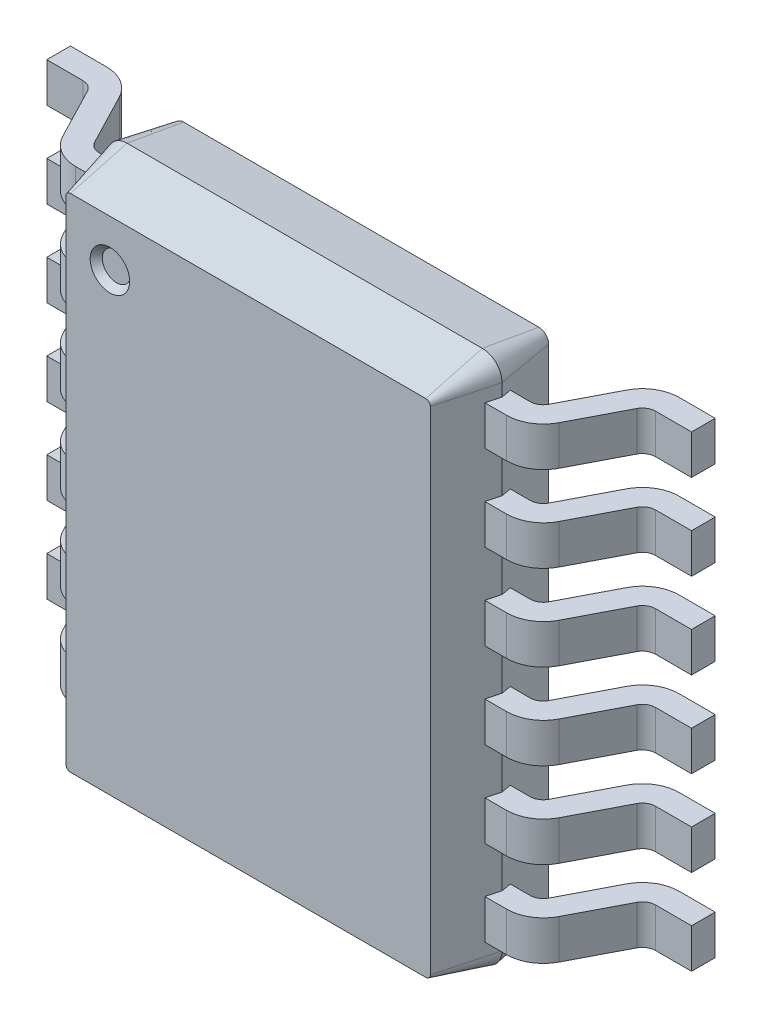
SolidWorks part; units mm, degrees
ref_plane "Спереди" through (0, 0, 0) normal (0, 0, 1) x (1, 0, 0)
ref_plane "Сверху" through (0, 0, 0) normal (0, 1, 0) x (1, 0, 0)
ref_plane "Справа" through (0, 0, 0) normal (1, 0, 0) x (0, 0, -1)
sketch "Эскиз1" plane through (0, 0, 0) normal (0, 0, 1) x (1, 0, 0)
  line L1 (-1.35, 2.02) -> (1.35, 2.02)
  line L2 (-1.5, 1.87) -> (-1.5, -1.87)
  line L3 (-1.35, -2.02) -> (1.35, -2.02)
  line L4 (1.5, 1.87) -> (1.5, -1.87)
  arc A0 (-1.5, 1.87) -> (-1.35, 2.02) centre (-1.35, 1.87) cw
  arc A1 (1.5, 1.87) -> (1.35, 2.02) centre (1.35, 1.87) ccw
  arc A2 (1.35, -2.02) -> (1.5, -1.87) centre (1.35, -1.87) ccw
  arc A3 (-1.5, -1.87) -> (-1.35, -2.02) centre (-1.35, -1.87) ccw
  point P0 (0, 0)
  dimension "D1" = 0.15
  dimension "D2" = 0.15
  dimension "D3" = 0.15
  dimension "D4" = 0.15
extrude "Вытянуть1" add sketch "Эскиз1" along normal blind 0.43 draft 15 and the other way blind 0.43 draft 10 from offset 0.67
sketch "Эскиз2" plane through (0, 0, 1.1) normal (0, 0, 1) x (1, 0, 0)
  circle A0 centre (-1.05, 1.55) radius 0.15
sketch "Эскиз3" plane through (0, 0, 0) normal (0, 1, 0) x (1, 0, 0)
  line L0 (-1.3754, -0.594) -> (-1.637, -0.594)
  line L1 (-1.3754, -0.7732) -> (-1.6374, -0.7732)
  line L2 (-1.3754, -0.594) -> (-1.3754, -0.7732)
  line L3 (-2.45, 0) -> (-2.1764, 0)
  line L4 (-2.45, 0) -> (-2.45, -0.18)
  line L5 (-1.9279, -0.1509) -> (-1.7258, -0.5401)
  line L6 (0, -0.24) -> (0, -1.1) construction
  line L7 (-2.45, -0.18) -> (-2.1764, -0.18)
  line L8 (-1.35, -0.24) -> (1.35, -0.24) construction
  line L9 (-2.0876, -0.2339) -> (-1.8859, -0.6223)
  line L10 (-1.35, -1.1) -> (1.35, -1.1) construction
  line L11 (2.0876, -0.2339) -> (1.8859, -0.6223)
  line L12 (2.45, -0.18) -> (2.1764, -0.18)
  line L13 (1.9279, -0.1509) -> (1.7258, -0.5401)
  line L14 (2.45, 0) -> (2.45, -0.18)
  line L15 (2.45, 0) -> (2.1764, 0)
  line L16 (1.3754, -0.594) -> (1.3754, -0.7732)
  line L17 (1.3754, -0.7732) -> (1.6374, -0.7732)
  line L18 (1.3754, -0.594) -> (1.637, -0.594)
  arc A0 (-1.637, -0.594) -> (-1.7258, -0.5401) centre (-1.637, -0.494) cw
  arc A1 (-1.8859, -0.6223) -> (-1.6374, -0.7732) centre (-1.6374, -0.4932) ccw
  arc A2 (-2.1764, 0) -> (-1.9279, -0.1509) centre (-2.1764, -0.28) cw
  arc A3 (-2.1764, -0.18) -> (-2.0876, -0.2339) centre (-2.1764, -0.28) cw
  arc A4 (2.1764, -0.18) -> (2.0876, -0.2339) centre (2.1764, -0.28) ccw
  arc A5 (2.1764, 0) -> (1.9279, -0.1509) centre (2.1764, -0.28) ccw
  arc A6 (1.8859, -0.6223) -> (1.6374, -0.7732) centre (1.6374, -0.4932) cw
  arc A7 (1.637, -0.594) -> (1.7258, -0.5401) centre (1.637, -0.494) ccw
extrude "Вытянуть2" add sketch "Эскиз3" along normal blind 0.15 and the other way blind 0.15 from offset 1.625
pattern_linear "Линейный массив1" count 6 spacing 0.65 along (0, -1, 0) of "Вытянуть2"
extrude "Вытянуть3" cut sketch "Эскиз2" against normal blind 0.05 draft 40
